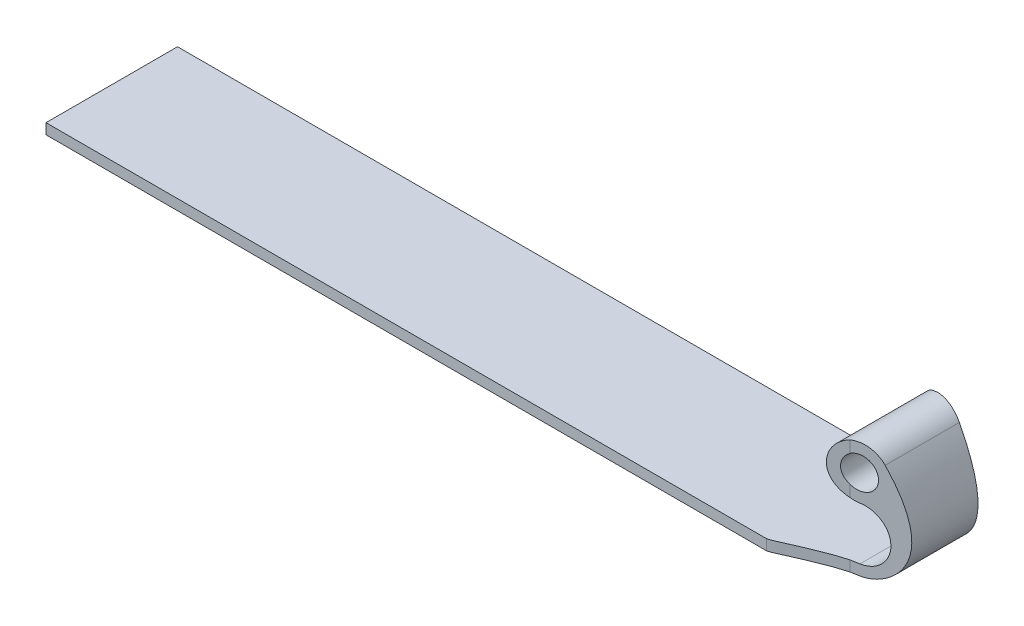
SolidWorks part; units mm, degrees
ref_plane "Front Plane" through (0, 0, 0) normal (0, 0, 1) x (1, 0, 0)
ref_plane "Top Plane" through (0, 0, 0) normal (0, 1, 0) x (1, 0, 0)
ref_plane "Right Plane" through (0, 0, 0) normal (1, 0, 0) x (0, 0, -1)
sketch "Sketch1" plane through (0, 0, 0) normal (0, 1, 0) x (1, 0, 0)
  line L1 (-38.1, -6.35) -> (38.1, -6.35)
  line L2 (-38.1, -6.35) -> (-38.1, 6.35)
  line L3 (-38.1, 6.35) -> (38.1, 6.35)
  line L4 (38.1, -6.35) -> (38.1, 6.35)
  line L5 (-38.1, -6.35) -> (38.1, 6.35) construction
  line L6 (-38.1, 6.35) -> (38.1, -6.35) construction
  point P0 (0, 0)
  dimension "D1" = 12.7
  dimension "D2" = 76.2
extrude "Boss-Extrude1" add sketch "Sketch1" along normal blind 1.016
sketch "Sketch2" plane through (0, 0, -6.35) normal (0, 0, -1) x (-1, 0, 0)
  line L1 (-38.1, 0) -> (38.1, 0) construction
  line L2 (-38.1, 0) -> (-40.0156, 0) construction
  line L3 (-40.0156, 0) -> (-42.8226, 1.8153) construction
  line L4 (-42.8226, 1.8153) -> (-43.8111, 4.9975) construction
  line L5 (-43.8111, 4.9975) -> (-40.1686, 10.1099) construction
  line L7 (-38.1, 1.016) -> (38.1, 1.016) construction
  line L8 (38.1, 1.016) -> (38.1, 0)
  line L9 (-38.1, 0) -> (38.1, 0)
  line L11 (38.1, 1.016) -> (38.1, 0) construction
  line L13 (-38.1, 1.016) -> (38.1, 1.016)
  arc A1 (-38.1, 6.096) -> (-40.1686, 10.1099) centre (-38.1, 8.636) ccw
  circle A2 centre (-38.1, 8.636) radius 1.524
  arc A6 (-38.1, 1.016) -> (-38.1, 6.096) centre (-38.1, 3.556) cw
  spline S0 degree 4 poles (-38.1, 0) (-40.0156, 0) (-42.8226, 1.8153) (-43.8111, 4.9975) (-40.1686, 10.1099) knots 0 0 0 0 0 1 1 1 1 1
  point P8 (-38.1, 1.016)
  dimension "D1" = 2.54
  dimension "D2" = 5.08
  dimension "D3" = 1.016
extrude "Boss-Extrude2" add sketch "Sketch2" against normal through all
sketch "Sketch3" plane through (0, 1.016, 0) normal (0, -1, 0) x (1, 0, 0)
  line L0 (24.4723, 6.35) -> (42.3541, 3.197)
  line L1 (-38.1, 6.35) -> (38.1, 6.35) construction
  line L2 (42.3541, 0) -> (38.1, 0) construction
  line L3 (42.3541, -6.35) -> (42.3541, 6.35) construction
  line L4 (38.1, 6.35) -> (38.1, -6.35) construction
  line L5 (24.4723, -6.35) -> (42.3541, -3.197)
  line L6 (24.4723, 6.35) -> (42.3541, 6.35)
  line L7 (42.3541, 6.35) -> (38.1, 6.35) construction
  line L8 (42.3541, 6.35) -> (42.3541, 3.197)
  line L9 (42.3541, -3.197) -> (42.3541, -6.35)
  line L10 (38.1, -6.35) -> (42.3541, -6.35) construction
  line L11 (42.3541, -6.35) -> (24.4723, -6.35)
  line L12 (39.2057, -3.7521) -> (36.3577, -3.8761) construction
  line L13 (36.3577, -3.8761) -> (31.9938, -6.35) construction
  line L14 (31.9938, -6.35) -> (31.4619, -6.35) construction
  line L15 (39.2057, 3.7521) -> (36.3577, 3.8761) construction
  line L16 (36.3577, 3.8761) -> (31.9938, 6.35) construction
  line L17 (31.9938, 6.35) -> (31.4619, 6.35) construction
  circle A0 centre (38.5441, 0) radius 3.81
  spline S0 degree 3 poles (39.2057, -3.7521) (36.3577, -3.8761) (31.9938, -6.35) (31.4619, -6.35) knots 0 0 0 0 1 1 1 1
  spline S1 degree 3 poles (39.2057, 3.7521) (36.3577, 3.8761) (31.9938, 6.35) (31.4619, 6.35) knots 0 0 0 0 1 1 1 1
  line M26 (38.1, 6.35) -> (38.1, -6.35)
  line M27 (38.1, -6.35) -> (-38.1, -6.35)
  dimension "D2" = 7.62
  dimension "D1" = 10
extrude "Cut-Extrude1" cut sketch "Sketch3" against normal through all and the other way blind 10 contours S0 L5 M26 M27 | L9 L11 L5 M26 | L6 L8 L0 M26 | L0 S1 L6 M26
